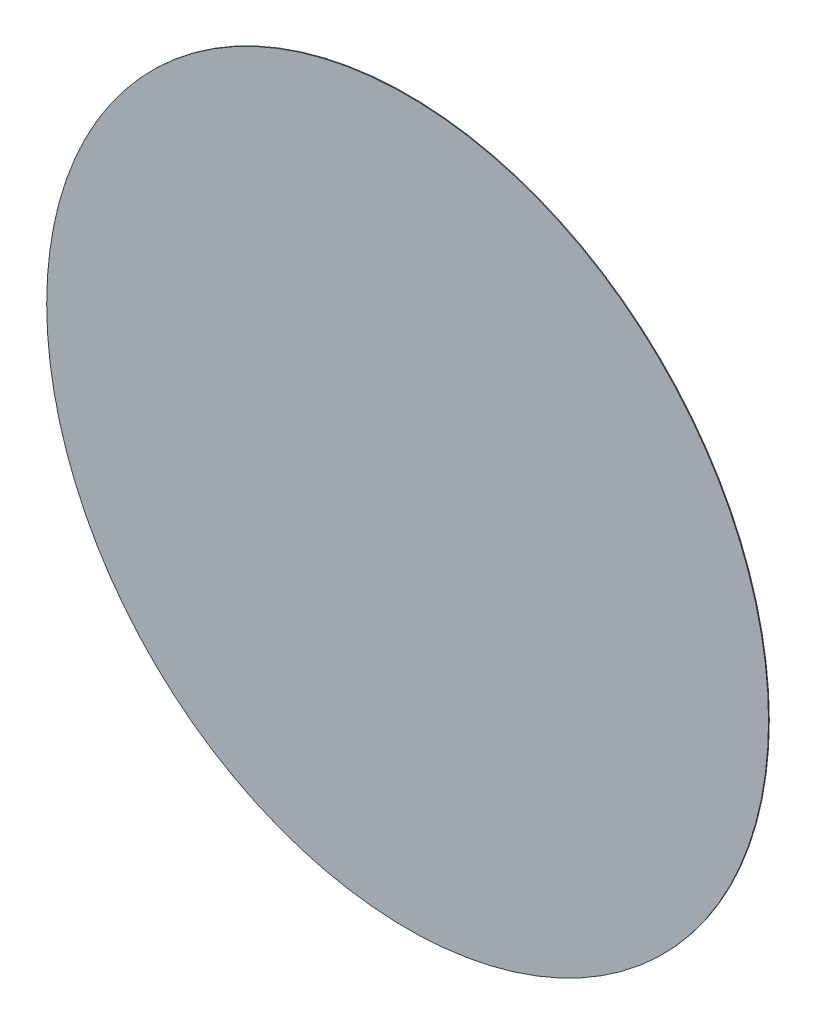
SolidWorks part; units mm, degrees
material "6061-T4 (SS)"
ref_plane "Front Plane" through (0, 0, 0) normal (0, 0, 1) x (1, 0, 0)
ref_plane "Top Plane" through (0, 0, 0) normal (0, 1, 0) x (1, 0, 0)
ref_plane "Right Plane" through (0, 0, 0) normal (1, 0, 0) x (0, 0, -1)
sketch "Sketch1" plane through (0, 0, 0) normal (0, 0, 1) x (1, 0, 0)
  circle A0 centre (0, 0) radius 4.75
  dimension "D1" = 9.5
extrude "Boss-Extrude1" add sketch "Sketch1" along normal blind 0.01
